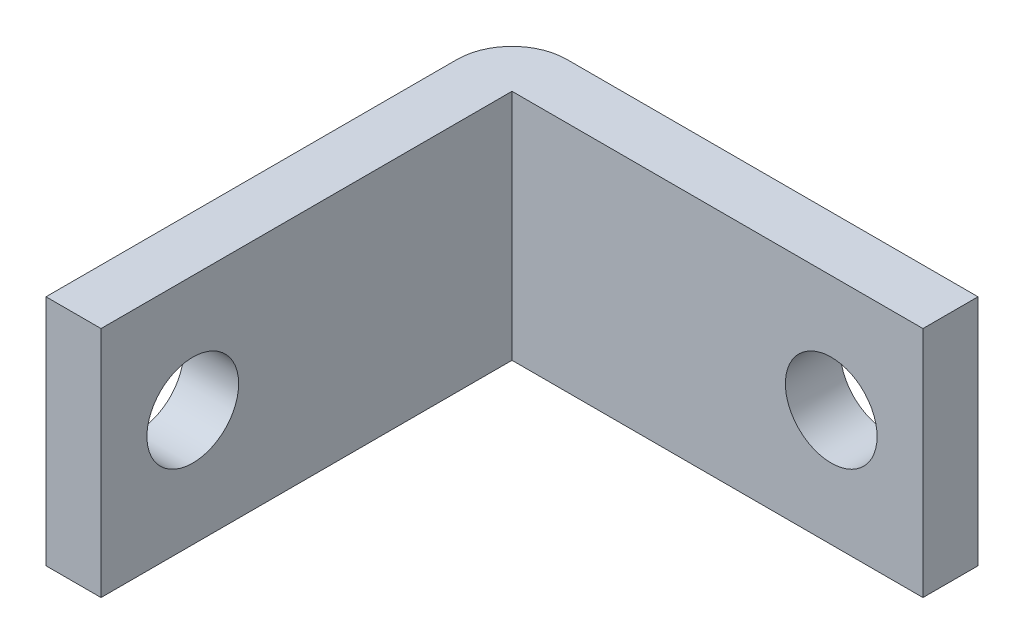
SolidWorks part; units mm, degrees
ref_plane "Alzado" through (0, 0, 0) normal (0, 0, 1) x (1, 0, 0)
ref_plane "Planta" through (0, 0, 0) normal (0, 1, 0) x (1, 0, 0)
ref_plane "Vista lateral" through (0, 0, 0) normal (1, 0, 0) x (0, 0, -1)
sketch "Croquis1" plane through (0, 0, 0) normal (0, 0, 1) x (1, 0, 0)
  line L1 (0, 0) -> (25.4, 0)
  line L2 (0, 0) -> (0, 12.7)
  line L3 (0, 12.7) -> (25.4, 12.7)
  line L4 (25.4, 0) -> (25.4, 12.7)
extrude "Saliente-Extruir1" add sketch "Croquis1" along normal blind 40
sketch "Croquis2" plane through (0, 12.7, 0) normal (0, 1, 0) x (1, 0, 0)
  line L0 (25.4, 0) -> (3, 0)
  line L1 (25.4, 0) -> (25.4, -3)
  line L2 (25.4, -40) -> (25.4, 0) construction
  line L3 (25.4, -3) -> (3, -3)
  line L4 (0, -40) -> (0, 0) construction
  line L5 (0, -3) -> (0, -25.4)
  line L6 (0, -25.4) -> (3, -25.4)
  line L7 (3, -25.4) -> (3, -3)
  line L9 (-8.3379, 7.4845) -> (32.5319, 7.4845)
  line L10 (-8.3379, 7.4845) -> (-8.3379, -43.9092)
  line L11 (-8.3379, -43.9092) -> (32.5319, -43.9092)
  line L12 (32.5319, 7.4845) -> (32.5319, -43.9092)
  arc A0 (0, -3) -> (3, 0) centre (3, -3) cw
extrude "Cortar-Extruir1" cut sketch "Croquis2" against normal blind 30
sketch "Croquis3" plane through (3, 0, 0) normal (1, 0, 0) x (0, 0, -1)
  circle A0 centre (-20.4, 6.35) radius 2.5
extrude "Cortar-Extruir2" cut sketch "Croquis3" against normal blind 30
sketch "Croquis4" plane through (0, 0, 3) normal (0, 0, 1) x (1, 0, 0)
  circle A0 centre (20.4, 6.35) radius 2.5
extrude "Cortar-Extruir3" cut sketch "Croquis4" against normal blind 30
